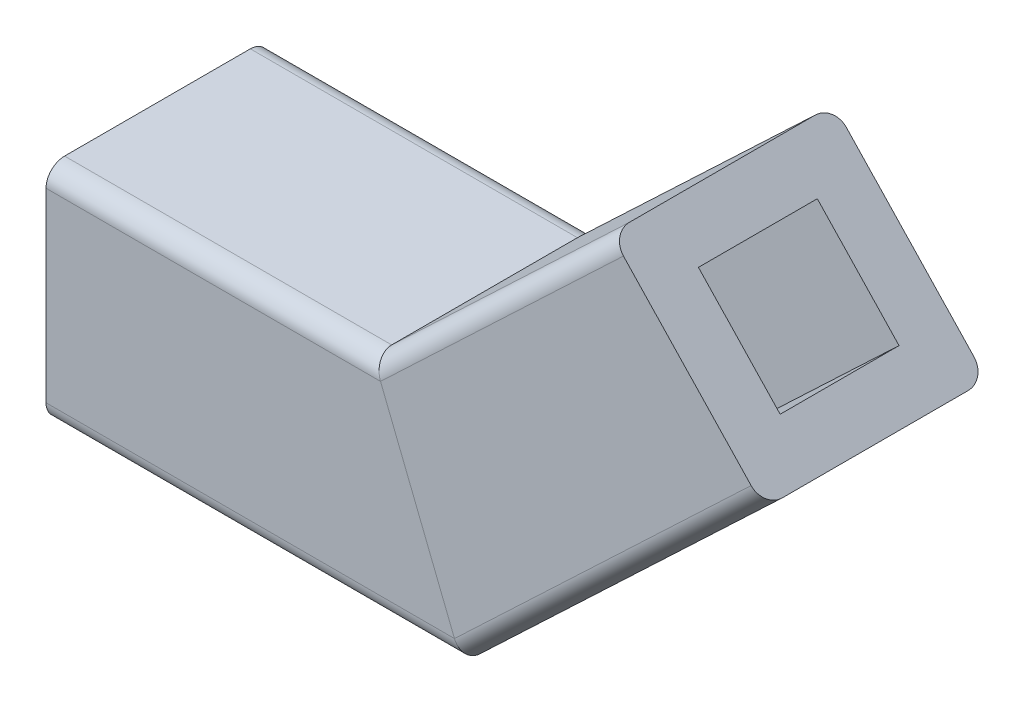
SolidWorks part; units mm, degrees
ref_plane "Front Plane" through (0, 0, 0) normal (0, 0, 1) x (1, 0, 0)
ref_plane "Top Plane" through (0, 0, 0) normal (0, 1, 0) x (1, 0, 0)
ref_plane "Right Plane" through (0, 0, 0) normal (1, 0, 0) x (0, 0, -1)
sketch "Sketch2" plane through (0, 0, 0) normal (0, 0, 1) x (1, 0, 0)
  line L0 (0, 0) -> (10, 0)
  line L1 (10, 0) -> (17.2621, 6.8747)
  dimension "D1" = 10
  dimension "D2" = 10
  dimension "D3" = 136.57
sketch "Sketch3" plane through (0, 0, 0) normal (1, 0, 0) x (0, 0, -1)
  line L1 (-1.6, -1.6) -> (1.6, -1.6)
  line L2 (-1.6, -1.6) -> (-1.6, 1.6)
  line L3 (-1.6, 1.6) -> (1.6, 1.6)
  line L4 (1.6, -1.6) -> (1.6, 1.6)
  line L5 (-1.6, -1.6) -> (1.6, 1.6) construction
  line L6 (-1.6, 1.6) -> (1.6, -1.6) construction
  line L7 (3, -3) -> (-3, -3)
  line L8 (3, -3) -> (3, 3)
  line L9 (3, 3) -> (-3, 3)
  line L10 (-3, -3) -> (-3, 3)
  line L11 (3, -3) -> (-3, 3) construction
  line L12 (3, 3) -> (-3, -3) construction
  point P0 (0, 0)
  dimension "D1" = 3.2
  dimension "D2" = 6
sweep "Sweep1" add profiles "Sketch3" path "Sketch2"
fillet "Fillet1" radius 0.5 8 edges at (15.2597, 0.848, -3) (5.5974, -3, -3) (12.0025, 6.0267, -3) (4.4026, 3, -3) (15.2597, 0.848, 3) (5.5974, -3, 3) (12.0025, 6.0267, 3) (4.4026, 3, 3)
